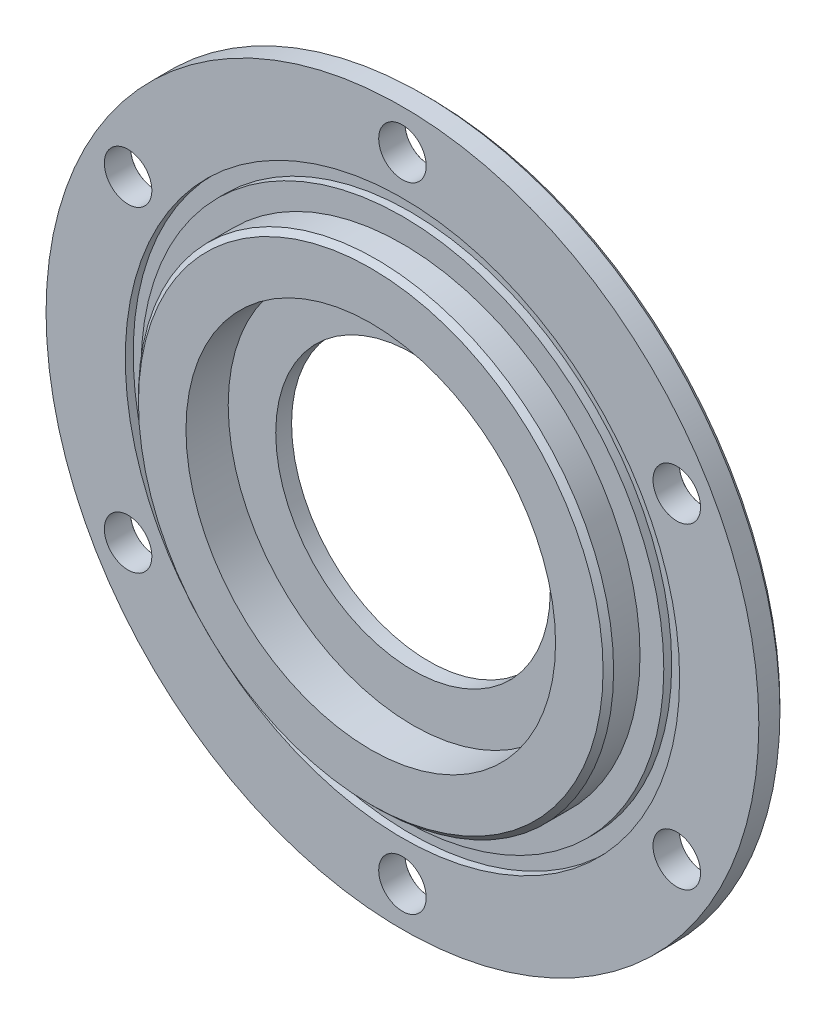
SolidWorks part; units mm, degrees
material "6061-T6 (SS)"
ref_plane "Piano frontale" through (0, 0, 0) normal (0, 0, 1) x (1, 0, 0)
ref_plane "Piano superiore" through (0, 0, 0) normal (0, 1, 0) x (1, 0, 0)
ref_plane "Piano destro" through (0, 0, 0) normal (1, 0, 0) x (0, 0, -1)
sketch "Schizzo1" plane through (0, 0, 0) normal (0, 0, 1) x (1, 0, 0)
  circle A0 centre (0, 0) radius 67.5
  dimension "D1" = 135
extrude "Estrusione-Estrusione1" add sketch "Schizzo1" along normal blind 5
sketch "Schizzo2" plane through (0, 0, 5) normal (0, 0, 1) x (1, 0, 0)
  circle A0 centre (0, 0) radius 45
  dimension "D1" = 90
extrude "Estrusione-Estrusione2" add sketch "Schizzo2" along normal blind 6
sketch "Schizzo3" plane through (0, 0, 11) normal (0, 0, 1) x (1, 0, 0)
  circle A0 centre (0, 0) radius 35
  dimension "D1" = 70
extrude "Taglio-Estrusione1" cut sketch "Schizzo3" against normal blind 8
sketch "Schizzo4" plane through (0, 0, 3) normal (0, 0, 1) x (1, 0, 0)
  circle A0 centre (0, 0) radius 26
  dimension "D1" = 52
extrude "Taglio-Estrusione2" cut sketch "Schizzo4" against normal through all
chamfer "Smusso1" distance 1 angle 45 2 edges at (45, 0, 11) (67.5, 0, 0)
sketch "Schizzo5" plane through (0, 0, 0) normal (0, 0, -1) x (-1, 0, 0)
  point P0 (0, 60)
  dimension "D1" = 60
hole_wizard "Foro per Vite M8-1" positions "Schizzo6" profile "Schizzo7" hole size "M8" standard "ISO" end condition through all
sketch "Schizzo6" plane through (0, 0, 0) normal (0, 0, -1) x (-1, 0, 0)
  point P0 (0, 60)
sketch "Schizzo7" plane through (0, 60, 0) normal (1, 0, 0) x (0, 1, 0)
  line L0 (0, 0) -> (0, 11)
  line L1 (0, 11) -> (4.5, 11)
  line L2 (4.5, 11) -> (4.5, 0.025)
  line L3 (4.5, 0.025) -> (4.525, 0)
  line L5 (4.525, 0) -> (0, 0)
  line L6 (-4.5, 0.025) -> (-4.525, 0) construction
  line L11 (0, -6.35) -> (0, 107.95) construction
  dimension "Thru Hole Dia." = 9
  dimension "Thru Hole Depth" = 11
  dimension "Near C'Sink Dia." = 9.05
  dimension "Near C'Sink Angle" = 90
pattern_circular "RipetizioneCircolare1" count 6 over 360 about axis through (0, 0, 0) along (0, 0, 1) of "Foro per Vite M8-1"
sketch "Schizzo8" plane through (0, 0, 5) normal (0, 0, 1) x (1, 0, 0)
  circle A0 centre (0, 0) radius 52.5
  circle A1 centre (0, 0) radius 49.5
  dimension "D1" = 105
  dimension "D2" = 99
extrude "Taglio-Estrusione3" cut sketch "Schizzo8" against normal blind 1.5
